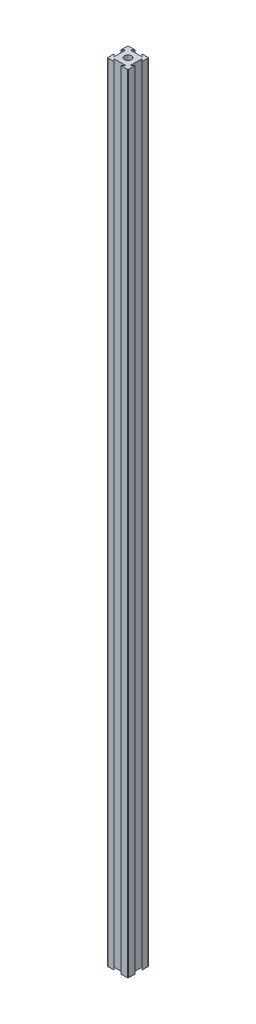
SolidWorks part; units mm, degrees
material "Alumina"
ref_plane "Front Plane" through (0, 0, 0) normal (0, 0, 1) x (1, 0, 0)
ref_plane "Top Plane" through (0, 0, 0) normal (0, 1, 0) x (1, 0, 0)
ref_plane "Right Plane" through (0, 0, 0) normal (1, 0, 0) x (0, 0, -1)
sketch "Sketch1" plane through (0, 0, 0) normal (0, 1, 0) x (1, 0, 0)
  line L0 (6.6667, 20) -> (4.285, 17.6183)
  line L1 (0, 0) -> (20, 0)
  line L2 (0, 0) -> (0, 20)
  line L3 (0, 20) -> (20, 20)
  line L4 (20, 0) -> (20, 20)
  line L5 (4.285, 17.6183) -> (15.715, 17.6183)
  line L6 (15.715, 17.6183) -> (13.3333, 20)
  line L7 (13.3333, 20) -> (6.6667, 20)
  line L8 (0, 10) -> (20, 10) construction
  line L9 (10, 20) -> (10, 0) construction
  line L10 (15.715, 2.3817) -> (13.3333, 0)
  line L11 (4.285, 2.3817) -> (15.715, 2.3817)
  line L12 (6.6667, 0) -> (4.285, 2.3817)
  line L13 (13.3333, 0) -> (6.6667, 0)
  line L14 (0, 13.3333) -> (2.3817, 15.715)
  line L15 (2.3817, 15.715) -> (2.3817, 4.285)
  line L16 (2.3817, 4.285) -> (0, 6.6667)
  line L17 (0, 6.6667) -> (0, 13.3333)
  line L18 (17.6183, 4.285) -> (20, 6.6667)
  line L19 (17.6183, 15.715) -> (17.6183, 4.285)
  line L20 (20, 13.3333) -> (17.6183, 15.715)
  line L21 (20, 6.6667) -> (20, 13.3333)
  circle A0 centre (10, 10) radius 3.3333
  dimension "D1" = 20
  dimension "D2" = 20
  dimension "D3" = 6.6667
  dimension "D4" = 6.6667
  dimension "D5" = 45
  dimension "D6" = 45
  dimension "D7" = 11.43
  dimension "D8" = 6.6667
  dimension "D9" = 6.6667
  dimension "D10" = 11.43
  dimension "D11" = 45
  dimension "D12" = 45
extrude "Boss-Extrude1" add sketch "Sketch1" along normal blind 762 contours L20 L4 L3 L6 L5 L0 L2 L14 L15 L16 L1 L12 L11 L10 L18 L19 A0
fillet "Fillet4" radius 0.508 4 edges at (0, 381, -20) (20, 381, -20) (0, 381, 0) (20, 381, 0)
